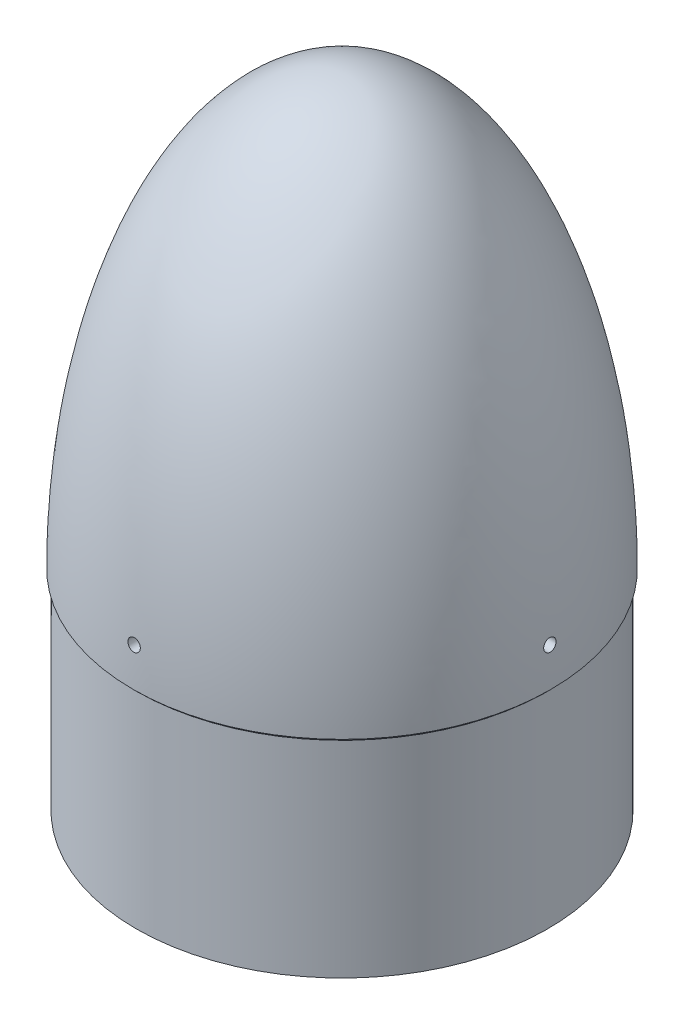
SolidWorks part; units mm, degrees
ref_plane "Front Plane" through (0, 0, 0) normal (0, 0, 1) x (1, 0, 0)
ref_plane "Top Plane" through (0, 0, 0) normal (0, 1, 0) x (1, 0, 0)
ref_plane "Right Plane" through (0, 0, 0) normal (1, 0, 0) x (0, 0, -1)
sketch "Sketch1" plane through (0, 0, 0) normal (0, 0, 1) x (1, 0, 0)
  line L3 (0, 0) -> (0, 202.3003) construction
  line L5 (0, 165.1) -> (0, 162.1028)
  line L12 (77.575, -80.518) -> (79.375, -80.518)
  line L13 (79.375, -80.518) -> (79.375, -1.143)
  line L14 (80.518, 0) -> (79.375, -1.143)
  line L15 (79.375, -1.143) -> (80.518, -1.143) construction
  line L17 (77.575, -0.3974) -> (77.575, -80.518)
  line L18 (77.575, -0.3974) -> (79.3153, 1.3429)
  line L19 (79.318, 0) -> (77.575, -1.743) construction
  ellipse E0 centre (0, 0) end of major axis (0, 162.1028) minor radius 79.318 (79.3153, 1.3429) -> (0, 162.1028) ccw
  ellipse E1 centre (0, 0) end of major axis (0, -165.1) minor radius 80.518 (80.518, 0) -> (0, 165.1) ccw
  dimension "D1" = 158.75
  dimension "D2" = 79.375
  dimension "D3" = 165.1
  dimension "D4" = 161.036
  dimension "D5" = 1.8
  dimension "D6" = 2.9972
  dimension "D7" = 45
  dimension "D8" = 1.2
  dimension "D9" = 1.8
revolve "Revolve1" add sketch "Sketch1" angle 360 about L5
ref_plane "Plane1" through (69.088, 0, 0) normal (-1, 0, 0) x (0, 0, 1)
sketch "Sketch6" plane through (0, 0, 0) normal (0, 0, 1) x (1, 0, 0)
  line L0 (73.66, 21.4703) -> (78.0342, 29.0467)
  line L1 (0, -200000) -> (0, 200202.3003) construction
  line L2 (77.575, -0.3974) -> (77.575, -18.5374)
  line L3 (73.66, 21.4703) -> (73.66, 17.1335)
  line L4 (77.575, -0.3974) -> (79.3153, 1.3429)
  line L5 (71.628, 21.082) -> (58.801, 21.082) construction
  line L6 (73.406, -80.518) -> (73.406, 21.082) construction
  line L9 (73.66, 17.1335) -> (73.66, -11.7564)
  line L10 (77.575, -0.3974) -> (-77.575, -0.3974) construction
  line L11 (73.66, -11.7564) -> (77.575, -18.5374)
  ellipse E0 centre (0, 0) end of major axis (0, 162.1028) minor radius 79.318 (79.3153, 1.3429) -> (0, 162.1028) ccw construction
  ellipse E1 centre (0, 0) end of major axis (0, 162.1028) minor radius 79.318 (79.0623, 13.0054) -> (78.0342, 29.0467) ccw
  ellipse E2 centre (0, 0) end of major axis (0, 162.1028) minor radius 79.318 (79.3153, 1.3429) -> (79.0623, 13.0054) ccw
  ellipse E3 centre (0, 0) end of major axis (0, -162.1028) minor radius 79.318 (79.3153, 1.3429) -> (79.0623, 13.0054) ccw
  ellipse E4 centre (0, 0) end of major axis (0, -162.1028) minor radius 79.318 (79.0623, 13.0054) -> (78.0342, 29.0467) ccw
  spline S0 degree 2 poles (55.7133, 13.0258) (55.7629, 12.319) (55.8125, 12.319) (55.8621, 12.319) (55.9117, 13.0258) (55.9614, 13.7325) (56.011, 14.732) (56.0606, 15.7315) (56.1102, 16.4382) (56.1598, 17.145) (56.2094, 17.145) (56.259, 17.145) (56.3086, 16.4382) (56.3582, 15.7315) (56.4078, 14.732) (56.4575, 13.7325) (56.5071, 13.0258) (56.5567, 12.319) (56.6063, 12.319) (56.6559, 12.319) (56.7055, 13.0258) (56.7551, 13.7325) (56.8047, 14.732) (56.8543, 15.7315) (56.9039, 16.4382) (56.9535, 17.145) (57.0032, 17.145) (57.0528, 17.145) (57.1024, 16.4382) (57.152, 15.7315) (57.2016, 14.732) (57.2512, 13.7325) (57.3008, 13.0258) (57.3504, 12.319) (57.4, 12.319) (57.4496, 12.319) (57.4992, 13.0258) (57.5489, 13.7325) (57.5985, 14.732) (57.6481, 15.7315) (57.6977, 16.4382) (57.7473, 17.145) (57.7969, 17.145) (57.8465, 17.145) (57.8961, 16.4382) (57.9457, 15.7315) (57.9953, 14.732) (58.045, 13.7325) (58.0946, 13.0258) (58.1442, 12.319) (58.1938, 12.319) (58.2434, 12.319) (58.293, 13.0258) (58.3426, 13.7325) (58.3922, 14.732) (58.4418, 15.7315) (58.4914, 16.4382) (58.541, 17.145) (58.5907, 17.145) (58.6403, 17.145) (58.6899, 16.4382) (58.7395, 15.7315) (58.7891, 14.732) (58.8387, 13.7325) (58.8883, 13.0258) (58.9379, 12.319) (58.9875, 12.319) (59.0371, 12.319) (59.0867, 13.0258) (59.1364, 13.7325) (59.186, 14.732) (59.2356, 15.7315) (59.2852, 16.4382) (59.3348, 17.145) (59.3844, 17.145) (59.434, 17.145) (59.4836, 16.4382) (59.5332, 15.7315) (59.5828, 14.732) (59.6325, 13.7325) (59.6821, 13.0258) (59.7317, 12.319) (59.7813, 12.319) (59.8309, 12.319) (59.8805, 13.0258) (59.9301, 13.7325) (59.9797, 14.732) (60.0293, 15.7315) (60.0789, 16.4382) (60.1285, 17.145) (60.1782, 17.145) (60.2278, 17.145) (60.2774, 16.4382) (60.327, 15.7315) (60.3766, 14.732) (60.4262, 13.7325) (60.4758, 13.0258) (60.5254, 12.319) (60.575, 12.319) (60.6246, 12.319) (60.6742, 13.0258) (60.7239, 13.7325) (60.7735, 14.732) (60.8231, 15.7315) (60.8727, 16.4382) (60.9223, 17.145) (60.9719, 17.145) (61.0215, 17.145) (61.0711, 16.4382) (61.1207, 15.7315) (61.1703, 14.732) (61.22, 13.7325) (61.2696, 13.0258) (61.3192, 12.319) (61.3688, 12.319) (61.4184, 12.319) (61.468, 13.0258) (61.5176, 13.7325) (61.5672, 14.732) (61.6168, 15.7315) (61.6664, 16.4382) (61.716, 17.145) (61.7657, 17.145) (61.8153, 17.145) (61.8649, 16.4382) (61.9145, 15.7315) (61.9641, 14.732) (62.0137, 13.7325) (62.0633, 13.0258) (62.1129, 12.319) (62.1625, 12.319) (62.2121, 12.319) (62.2617, 13.0258) (62.3114, 13.7325) (62.361, 14.732) (62.4106, 15.7315) (62.4602, 16.4382) (62.5098, 17.145) (62.5594, 17.145) (62.609, 17.145) (62.6586, 16.4382) (62.7082, 15.7315) (62.7578, 14.732) (62.8075, 13.7325) (62.8571, 13.0258) (62.9067, 12.319) (62.9563, 12.319) (63.0059, 12.319) (63.0555, 13.0258) (63.1051, 13.7325) (63.1547, 14.732) (63.2043, 15.7315) (63.2539, 16.4382) (63.3035, 17.145) (63.3532, 17.145) (63.4028, 17.145) (63.4524, 16.4382) (63.502, 15.7315) (63.5516, 14.732) (63.6012, 13.7325) (63.6508, 13.0258) (63.7004, 12.319) (63.75, 12.319) (63.7996, 12.319) (63.8492, 13.0258) (63.8989, 13.7325) (63.9485, 14.732) (63.9981, 15.7315) (64.0477, 16.4382) (64.0973, 17.145) (64.1469, 17.145) (64.1965, 17.145) (64.2461, 16.4382) (64.2957, 15.7315) (64.3453, 14.732) (64.395, 13.7325) (64.4446, 13.0258) (64.4942, 12.319) (64.5438, 12.319) (64.5934, 12.319) (64.643, 13.0258) (64.6926, 13.7325) (64.7422, 14.732) (64.7918, 15.7315) (64.8414, 16.4382) (64.891, 17.145) (64.9407, 17.145) (64.9903, 17.145) (65.0399, 16.4382) (65.0895, 15.7315) (65.1391, 14.732) (65.1887, 13.7325) (65.2383, 13.0258) (65.2879, 12.319) (65.3375, 12.319) (65.3871, 12.319) (65.4367, 13.0258) (65.4864, 13.7325) (65.536, 14.732) (65.5856, 15.7315) (65.6352, 16.4382) (65.6848, 17.145) (65.7344, 17.145) (65.784, 17.145) (65.8336, 16.4382) (65.8832, 15.7315) (65.9328, 14.732) (65.9825, 13.7325) (66.0321, 13.0258) (66.0817, 12.319) (66.1313, 12.319) (66.1809, 12.319) (66.2305, 13.0258) (66.2801, 13.7325) (66.3297, 14.732) (66.3793, 15.7315) (66.4289, 16.4382) (66.4785, 17.145) (66.5282, 17.145) (66.5778, 17.145) (66.6274, 16.4382) (66.677, 15.7315) (66.7266, 14.732) (66.7762, 13.7325) (66.8258, 13.0258) (66.8754, 12.319) (66.925, 12.319) (66.9746, 12.319) (67.0242, 13.0258) (67.0739, 13.7325) (67.1235, 14.732) (67.1731, 15.7315) (67.2227, 16.4382) (67.2723, 17.145) (67.3219, 17.145) (67.3715, 17.145) (67.4211, 16.4382) (67.4707, 15.7315) (67.5203, 14.732) (67.57, 13.7325) (67.6196, 13.0258) (67.6692, 12.319) (67.7188, 12.319) (67.7684, 12.319) (67.818, 13.0258) (67.8676, 13.7325) (67.9172, 14.732) (67.9668, 15.7315) (68.0164, 16.4382) (68.066, 17.145) (68.1157, 17.145) (68.1653, 17.145) (68.2149, 16.4382) (68.2645, 15.7315) (68.3141, 14.732) (68.3637, 13.7325) (68.4133, 13.0258) (68.4629, 12.319) (68.5125, 12.319) (68.5621, 12.319) (68.6117, 13.0258) (68.6614, 13.7325) (68.711, 14.732) (68.7606, 15.7315) (68.8102, 16.4382) (68.8598, 17.145) (68.9094, 17.145) (68.959, 17.145) (69.0086, 16.4382) (69.0582, 15.7315) (69.1078, 14.732) (69.1575, 13.7325) (69.2071, 13.0258) (69.2567, 12.319) (69.3063, 12.319) (69.3559, 12.319) (69.4055, 13.0258) (69.4551, 13.7325) (69.5047, 14.732) (69.5543, 15.7315) (69.6039, 16.4382) (69.6535, 17.145) (69.7032, 17.145) (69.7528, 17.145) (69.8024, 16.4382) (69.852, 15.7315) (69.9016, 14.732) (69.9512, 13.7325) (70.0008, 13.0258) (70.0504, 12.319) (70.1, 12.319) (70.1496, 12.319) (70.1992, 13.0258) (70.2489, 13.7325) (70.2985, 14.732) (70.3481, 15.7315) (70.3977, 16.4382) (70.4473, 17.145) (70.4969, 17.145) (70.5465, 17.145) (70.5961, 16.4382) (70.6457, 15.7315) (70.6953, 14.732) (70.745, 13.7325) (70.7946, 13.0258) (70.8442, 12.319) (70.8938, 12.319) (70.9434, 12.319) (70.993, 13.0258) (71.0426, 13.7325) (71.0922, 14.732) (71.1418, 15.7315) (71.1914, 16.4382) (71.241, 17.145) (71.2907, 17.145) (71.3403, 17.145) (71.3899, 16.4382) (71.4395, 15.7315) (71.4891, 14.732) (71.5387, 13.7325) (71.5883, 13.0258) (71.6379, 12.319) (71.6875, 12.319) (71.7371, 12.319) (71.7867, 13.0258) (71.8364, 13.7325) (71.886, 14.732) (71.9356, 15.7315) (71.9852, 16.4382) (72.0348, 17.145) (72.0844, 17.145) (72.134, 17.145) (72.1836, 16.4382) (72.2332, 15.7315) (72.2828, 14.732) (72.3325, 13.7325) (72.3821, 13.0258) (72.4317, 12.319) (72.4813, 12.319) (72.5309, 12.319) (72.5805, 13.0258) (72.6301, 13.7325) (72.6797, 14.732) (72.7293, 15.7315) (72.7789, 16.4382) (72.8285, 17.145) (72.8782, 17.145) (72.9278, 17.145) (72.9774, 16.4382) (73.027, 15.7315) (73.0766, 14.732) (73.1262, 13.7325) (73.1758, 13.0258) (73.2254, 12.319) (73.275, 12.319) (73.3246, 12.319) (73.3742, 13.0258) (73.4239, 13.7325) (73.4735, 14.732) (73.5231, 15.7315) (73.5727, 16.4382) (73.6223, 17.145) (73.6719, 17.145) (73.7215, 17.145) (73.7711, 16.4382) (73.8207, 15.7315) (73.8703, 14.732) (73.92, 13.7325) (73.9696, 13.0258) (74.0192, 12.319) (74.0688, 12.319) (74.1184, 12.319) (74.168, 13.0258) (74.2176, 13.7325) (74.2672, 14.732) (74.3168, 15.7315) (74.3664, 16.4382) (74.416, 17.145) (74.4657, 17.145) (74.5153, 17.145) (74.5649, 16.4382) (74.6145, 15.7315) (74.6641, 14.732) (74.7137, 13.7325) (74.7633, 13.0258) (74.8129, 12.319) (74.8625, 12.319) (74.9121, 12.319) (74.9617, 13.0258) (75.0114, 13.7325) (75.061, 14.732) (75.1106, 15.7315) (75.1602, 16.4382) (75.2098, 17.145) (75.2594, 17.145) (75.309, 17.145) (75.3586, 16.4382) (75.4082, 15.7315) (75.4578, 14.732) (75.5075, 13.7325) (75.5571, 13.0258) (75.6067, 12.319) (75.6563, 12.319) (75.7059, 12.319) (75.7555, 13.0258) (75.8051, 13.7325) (75.8547, 14.732) (75.9043, 15.7315) (75.9539, 16.4382) (76.0035, 17.145) (76.0532, 17.145) (76.1028, 17.145) (76.1524, 16.4382) (76.202, 15.7315) (76.2516, 14.732) (76.3012, 13.7325) (76.3508, 13.0258) (76.4004, 12.319) (76.45, 12.319) (76.4996, 12.319) (76.5492, 13.0258) (76.5989, 13.7325) (76.6485, 14.732) (76.6981, 15.7315) (76.7477, 16.4382) (76.7973, 17.145) (76.8469, 17.145) (76.8965, 17.145) (76.9461, 16.4382) (76.9957, 15.7315) (77.0453, 14.732) (77.095, 13.7325) (77.1446, 13.0258) (77.1942, 12.319) (77.2438, 12.319) (77.2934, 12.319) (77.343, 13.0258) (77.3926, 13.7325) (77.4422, 14.732) (77.4918, 15.7315) (77.5414, 16.4382) (77.591, 17.145) (77.6407, 17.145) (77.6903, 17.145) (77.7399, 16.4382) (77.7895, 15.7315) (77.8391, 14.732) (77.8887, 13.7325) (77.9383, 13.0258) (77.9879, 12.319) (78.0375, 12.319) (78.0871, 12.319) (78.1367, 13.0258) (78.1864, 13.7325) (78.236, 14.732) (78.2856, 15.7315) (78.3352, 16.4382) (78.3848, 17.145) (78.4344, 17.145) (78.484, 17.145) (78.5336, 16.4382) (78.5832, 15.7315) (78.6328, 14.732) (78.6825, 13.7325) (78.7321, 13.0258) (78.7817, 12.319) (78.8313, 12.319) (78.8809, 12.319) (78.9305, 13.0258) (78.9801, 13.7325) (79.0297, 14.732) (79.0793, 15.7315) (79.1289, 16.4382) (79.1785, 17.145) (79.2282, 17.145) (79.2778, 17.145) (79.3274, 16.4382) (79.377, 15.7315) (79.4266, 14.732) (79.4762, 13.7325) (79.5258, 13.0258) (79.5754, 12.319) (79.625, 12.319) (79.6746, 12.319) (79.7242, 13.0258) (79.7739, 13.7325) (79.8235, 14.732) (79.8731, 15.7315) (79.9227, 16.4382) (79.9723, 17.145) (80.0219, 17.145) (80.0715, 17.145) (80.1211, 16.4382) (80.1707, 15.7315) (80.2203, 14.732) (80.27, 13.7325) (80.3196, 13.0258) (80.3692, 12.319) (80.4188, 12.319) (80.4684, 12.319) (80.518, 13.0258) knots 0.049242 0.049242 0.049242 0.05303 0.05303 0.056818 0.056818 0.060606 0.060606 0.064394 0.064394 0.068182 0.068182 0.07197 0.07197 0.075758 0.075758 0.079545 0.079545 0.083333 0.083333 0.087121 0.087121 0.090909 0.090909 0.094697 0.094697 0.098485 0.098485 0.102273 0.102273 0.106061 0.106061 0.109848 0.109848 0.113636 0.113636 0.117424 0.117424 0.121212 0.121212 0.125 0.125 0.128788 0.128788 0.132576 0.132576 0.136364 0.136364 0.140152 0.140152 0.143939 0.143939 0.147727 0.147727 0.151515 0.151515 0.155303 0.155303 0.159091 0.159091 0.162879 0.162879 0.166667 0.166667 0.170455 0.170455 0.174242 0.174242 0.17803 0.17803 0.181818 0.181818 0.185606 0.185606 0.189394 0.189394 0.193182 0.193182 0.19697 0.19697 0.200758 0.200758 0.204545 0.204545 0.208333 0.208333 0.212121 0.212121 0.215909 0.215909 0.219697 0.219697 0.223485 0.223485 0.227273 0.227273 0.231061 0.231061 0.234848 0.234848 0.238636 0.238636 0.242424 0.242424 0.246212 0.246212 0.25 0.25 0.253788 0.253788 0.257576 0.257576 0.261364 0.261364 0.265152 0.265152 0.268939 0.268939 0.272727 0.272727 0.276515 0.276515 0.280303 0.280303 0.284091 0.284091 0.287879 0.287879 0.291667 0.291667 0.295455 0.295455 0.299242 0.299242 0.30303 0.30303 0.306818 0.306818 0.310606 0.310606 0.314394 0.314394 0.318182 0.318182 0.32197 0.32197 0.325758 0.325758 0.329545 0.329545 0.333333 0.333333 0.337121 0.337121 0.340909 0.340909 0.344697 0.344697 0.348485 0.348485 0.352273 0.352273 0.356061 0.356061 0.359848 0.359848 0.363636 0.363636 0.367424 0.367424 0.371212 0.371212 0.375 0.375 0.378788 0.378788 0.382576 0.382576 0.386364 0.386364 0.390152 0.390152 0.393939 0.393939 0.397727 0.397727 0.401515 0.401515 0.405303 0.405303 0.409091 0.409091 0.412879 0.412879 0.416667 0.416667 0.420455 0.420455 0.424242 0.424242 0.42803 0.42803 0.431818 0.431818 0.435606 0.435606 0.439394 0.439394 0.443182 0.443182 0.44697 0.44697 0.450758 0.450758 0.454545 0.454545 0.458333 0.458333 0.462121 0.462121 0.465909 0.465909 0.469697 0.469697 0.473485 0.473485 0.477273 0.477273 0.481061 0.481061 0.484848 0.484848 0.488636 0.488636 0.492424 0.492424 0.496212 0.496212 0.5 0.5 0.503788 0.503788 0.507576 0.507576 0.511364 0.511364 0.515152 0.515152 0.518939 0.518939 0.522727 0.522727 0.526515 0.526515 0.530303 0.530303 0.534091 0.534091 0.537879 0.537879 0.541667 0.541667 0.545455 0.545455 0.549242 0.549242 0.55303 0.55303 0.556818 0.556818 0.560606 0.560606 0.564394 0.564394 0.568182 0.568182 0.57197 0.57197 0.575758 0.575758 0.579545 0.579545 0.583333 0.583333 0.587121 0.587121 0.590909 0.590909 0.594697 0.594697 0.598485 0.598485 0.602273 0.602273 0.606061 0.606061 0.609848 0.609848 0.613636 0.613636 0.617424 0.617424 0.621212 0.621212 0.625 0.625 0.628788 0.628788 0.632576 0.632576 0.636364 0.636364 0.640152 0.640152 0.643939 0.643939 0.647727 0.647727 0.651515 0.651515 0.655303 0.655303 0.659091 0.659091 0.662879 0.662879 0.666667 0.666667 0.670455 0.670455 0.674242 0.674242 0.67803 0.67803 0.681818 0.681818 0.685606 0.685606 0.689394 0.689394 0.693182 0.693182 0.69697 0.69697 0.700758 0.700758 0.704545 0.704545 0.708333 0.708333 0.712121 0.712121 0.715909 0.715909 0.719697 0.719697 0.723485 0.723485 0.727273 0.727273 0.731061 0.731061 0.734848 0.734848 0.738636 0.738636 0.742424 0.742424 0.746212 0.746212 0.75 0.75 0.753788 0.753788 0.757576 0.757576 0.761364 0.761364 0.765152 0.765152 0.768939 0.768939 0.772727 0.772727 0.776515 0.776515 0.780303 0.780303 0.784091 0.784091 0.787879 0.787879 0.791667 0.791667 0.795455 0.795455 0.799242 0.799242 0.80303 0.80303 0.806818 0.806818 0.810606 0.810606 0.814394 0.814394 0.818182 0.818182 0.82197 0.82197 0.825758 0.825758 0.829545 0.829545 0.833333 0.833333 0.837121 0.837121 0.840909 0.840909 0.844697 0.844697 0.848485 0.848485 0.852273 0.852273 0.856061 0.856061 0.859848 0.859848 0.863636 0.863636 0.867424 0.867424 0.871212 0.871212 0.875 0.875 0.878788 0.878788 0.882576 0.882576 0.886364 0.886364 0.890152 0.890152 0.893939 0.893939 0.897727 0.897727 0.901515 0.901515 0.905303 0.905303 0.909091 0.909091 0.912879 0.912879 0.916667 0.916667 0.920455 0.920455 0.924242 0.924242 0.92803 0.92803 0.931818 0.931818 0.935606 0.935606 0.939394 0.939394 0.943182 0.943182 0.94697 0.94697 0.950758 0.950758 0.954545 0.954545 0.958333 0.958333 0.962121 0.962121 0.965909 0.965909 0.969697 0.969697 0.973485 0.973485 0.977273 0.977273 0.981061 0.981061 0.984848 0.984848 0.988636 0.988636 0.992424 0.992424 0.996212 0.996212 0.996212 weights 1 0.92388 1 0.92388 1 0.92388 1 0.92388 1 0.92388 1 0.92388 1 0.92388 1 0.92388 1 0.92388 1 0.92388 1 0.92388 1 0.92388 1 0.92388 1 0.92388 1 0.92388 1 0.92388 1 0.92388 1 0.92388 1 0.92388 1 0.92388 1 0.92388 1 0.92388 1 0.92388 1 0.92388 1 0.92388 1 0.92388 1 0.92388 1 0.92388 1 0.92388 1 0.92388 1 0.92388 1 0.92388 1 0.92388 1 0.92388 1 0.92388 1 0.92388 1 0.92388 1 0.92388 1 0.92388 1 0.92388 1 0.92388 1 0.92388 1 0.92388 1 0.92388 1 0.92388 1 0.92388 1 0.92388 1 0.92388 1 0.92388 1 0.92388 1 0.92388 1 0.92388 1 0.92388 1 0.92388 1 0.92388 1 0.92388 1 0.92388 1 0.92388 1 0.92388 1 0.92388 1 0.92388 1 0.92388 1 0.92388 1 0.92388 1 0.92388 1 0.92388 1 0.92388 1 0.92388 1 0.92388 1 0.92388 1 0.92388 1 0.92388 1 0.92388 1 0.92388 1 0.92388 1 0.92388 1 0.92388 1 0.92388 1 0.92388 1 0.92388 1 0.92388 1 0.92388 1 0.92388 1 0.92388 1 0.92388 1 0.92388 1 0.92388 1 0.92388 1 0.92388 1 0.92388 1 0.92388 1 0.92388 1 0.92388 1 0.92388 1 0.92388 1 0.92388 1 0.92388 1 0.92388 1 0.92388 1 0.92388 1 0.92388 1 0.92388 1 0.92388 1 0.92388 1 0.92388 1 0.92388 1 0.92388 1 0.92388 1 0.92388 1 0.92388 1 0.92388 1 0.92388 1 0.92388 1 0.92388 1 0.92388 1 0.92388 1 0.92388 1 0.92388 1 0.92388 1 0.92388 1 0.92388 1 0.92388 1 0.92388 1 0.92388 1 0.92388 1 0.92388 1 0.92388 1 0.92388 1 0.92388 1 0.92388 1 0.92388 1 0.92388 1 0.92388 1 0.92388 1 0.92388 1 0.92388 1 0.92388 1 0.92388 1 0.92388 1 0.92388 1 0.92388 1 0.92388 1 0.92388 1 0.92388 1 0.92388 1 0.92388 1 0.92388 1 0.92388 1 0.92388 1 0.92388 1 0.92388 1 0.92388 1 0.92388 1 0.92388 1 0.92388 1 0.92388 1 0.92388 1 0.92388 1 0.92388 1 0.92388 1 0.92388 1 0.92388 1 0.92388 1 0.92388 1 0.92388 1 0.92388 1 0.92388 1 0.92388 1 0.92388 1 0.92388 1 0.92388 1 0.92388 1 0.92388 1 0.92388 1 0.92388 1 0.92388 1 0.92388 1 0.92388 1 0.92388 1 0.92388 1 0.92388 1 0.92388 1 0.92388 1 0.92388 1 0.92388 1 0.92388 1 0.92388 1 0.92388 1 0.92388 1 0.92388 1 0.92388 1 0.92388 1 0.92388 1 0.92388 1 0.92388 1 0.92388 1 0.92388 1 0.92388 1 0.92388 1 0.92388 1 0.92388 1 0.92388 1 0.92388 1 0.92388 1 0.92388 1 0.92388 1 0.92388 1 0.92388 1 0.92388 1 0.92388 1 0.92388 1 0.92388 1 0.92388 1 0.92388 1 0.92388 1 0.92388 1 0.92388 1 0.92388 1 0.92388 1 0.92388 1 0.92388 1 0.92388 1 0.92388 1 0.92388 1 0.92388 1 0.92388 1 0.92388 1 0.92388 1 0.92388 1 0.92388 1 0.92388 1 0.92388 1 0.92388 1 0.92388 1 0.92388 1 0.92388 1 0.92388 1 0.92388 1 0.92388 1 0.92388 1 0.92388 1 0.92388 1 0.92388 1 0.92388 1 0.92388 1 0.92388 1 0.92388 1 0.92388 1 0.92388 1 0.92388 1 construction
  point P14 (79.0876, 13.0054)
  point P23 (0, 0)
  point P24 (73.5738, 16.4534)
  point P40 (0, 0)
  point P44 (0, 0)
  point P47 (0, 0)
  point P49 (73.66, -11.7564)
  dimension "D1" = 60
  dimension "D2" = 0.254
  dimension "D3" = 60
extrude "Boss-Extrude1" add sketch "Sketch6" against normal up to vertex and the other way up to surface
sketch "Sketch3" plane through (71.628, 0, 0) normal (-1, 0, 0) x (0, 0, 1)
  circle A0 centre (0, 14.732) radius 2.3813
  dimension "D1" = 4.7625
extrude "Cut-Extrude1" cut sketch "Sketch3" against normal through all contours A0
pattern_circular "CirPattern1" count 4 over 360 about axis through (0, 0, 0) along (0, 1, 0) of "Cut-Extrude1", "Boss-Extrude1"
sketch "Sketch7" plane through (0, -74.168, 0) normal (0, 0, 1) x (1, 0, 0)
  line L0 (73.66, 95.6383) -> (78.0342, 103.2147)
  line L1 (73.66, 95.6383) -> (72.8301, 138.3784)
  ellipse E0 centre (0, 74.168) end of major axis (0, -87.9348) minor radius 79.318 (78.0342, 103.2147) -> (72.8301, 138.3784) ccw
  ellipse E1 centre (0, 74.168) end of major axis (0, 236.2708) minor radius 79.318 (79.3153, 75.5109) -> (0, 236.2708) ccw construction
extrude "Boss-Extrude2" add sketch "Sketch7" along normal mid plane 12.7
sketch "Sketch8" plane through (74.049, 1.4379, 0) normal (-0.9998, -0.0194, 0) x (0, 0, 1)
  line L0 (0, 61.4124) -> (0, 50.8618)
